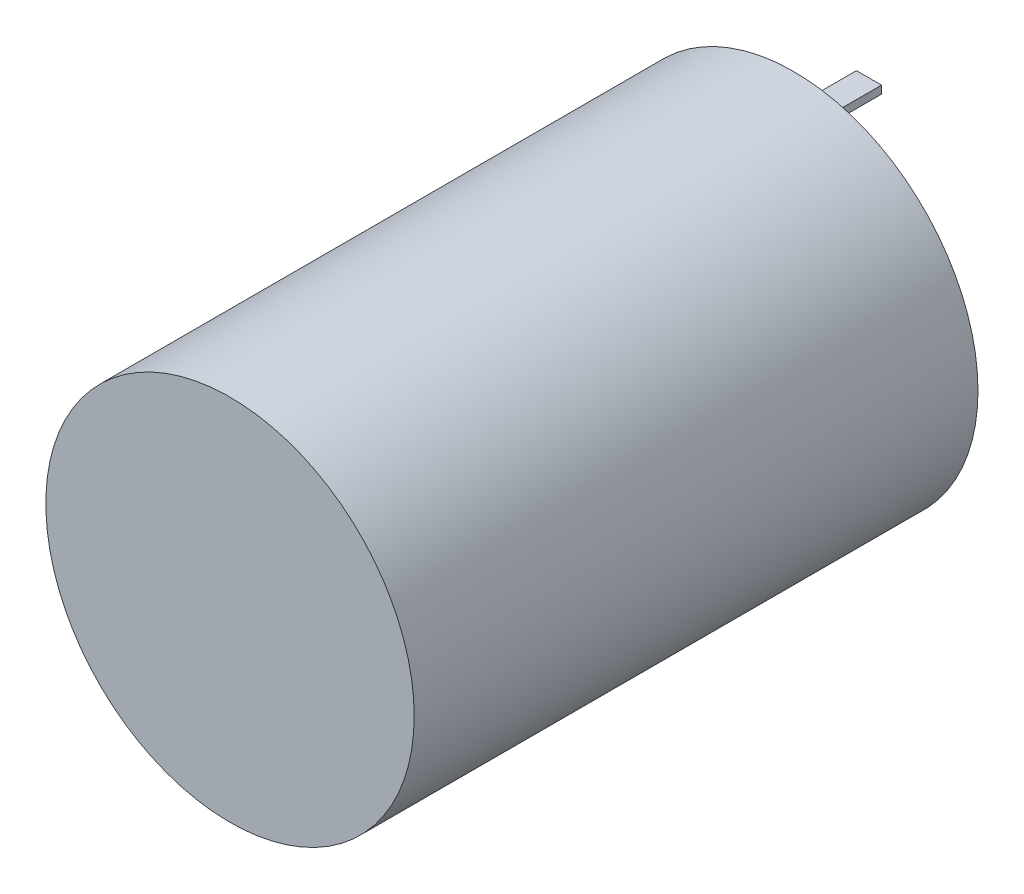
SolidWorks part; units mm, degrees
ref_plane "Front Plane" through (0, 0, 0) normal (0, 0, 1) x (1, 0, 0)
ref_plane "Top Plane" through (0, 0, 0) normal (0, 1, 0) x (1, 0, 0)
ref_plane "Right Plane" through (0, 0, 0) normal (1, 0, 0) x (0, 0, -1)
sketch "Sketch1" plane through (0, 0, 0) normal (0, 0, 1) x (1, 0, 0)
  circle A0 centre (0, 0) radius 18.669
  dimension "D1" = 37.338
extrude "Boss-Extrude1" add sketch "Sketch1" along normal blind 57.15
sketch "Sketch2" plane through (0, 0, 0) normal (0, 0, -1) x (-1, 0, 0)
  line L1 (-1.27, 14.3034) -> (1.27, 14.3034)
  line L2 (-1.27, 14.3034) -> (-1.27, 13.5096)
  line L3 (-1.27, 13.5096) -> (1.27, 13.5096)
  line L4 (1.27, 14.3034) -> (1.27, 13.5096)
  line L5 (-1.27, 14.3034) -> (1.27, 13.5096) construction
  line L6 (-1.27, 13.5096) -> (1.27, 14.3034) construction
  line L7 (-1.27, -13.5096) -> (1.27, -13.5096)
  line L8 (-1.27, -13.5096) -> (-1.27, -14.3034)
  line L9 (-1.27, -14.3034) -> (1.27, -14.3034)
  line L10 (1.27, -13.5096) -> (1.27, -14.3034)
  line L11 (-1.27, -13.5096) -> (1.27, -14.3034) construction
  line L12 (-1.27, -14.3034) -> (1.27, -13.5096) construction
  circle A0 centre (0, 0) radius 13.9065 construction
  circle A1 centre (0, 0) radius 18.669
  circle A2 centre (0, 0) radius 18.669
  point P1 (0, 13.9065)
  point P9 (0, -13.9065)
  dimension "D2" = 4.7625
  dimension "D3" = 2.54
  dimension "D4" = 0.7937
  dimension "D1" = 0
extrude "Boss-Extrude2" add sketch "Sketch2" along normal blind 7.62 contours L4 L1 L2 L3 | L10 L7 L8 L9
